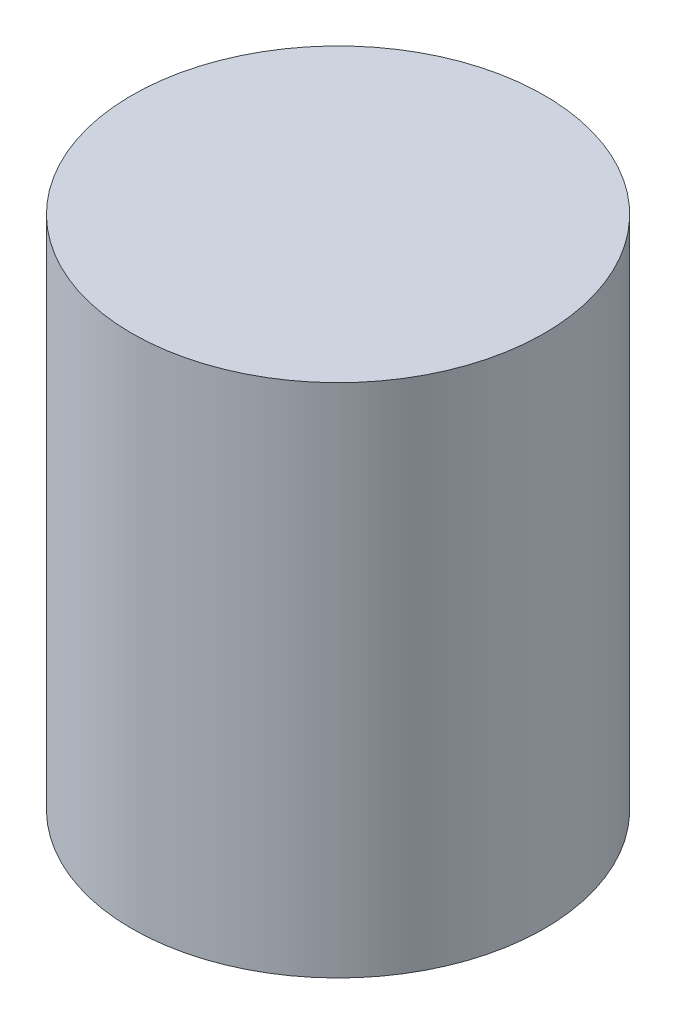
SolidWorks part; units mm, degrees
material "6061-T6 (SS)"
ref_plane "Front Plane" through (0, 0, 0) normal (0, 0, 1) x (1, 0, 0)
ref_plane "Top Plane" through (0, 0, 0) normal (0, 1, 0) x (1, 0, 0)
ref_plane "Right Plane" through (0, 0, 0) normal (1, 0, 0) x (0, 0, -1)
sketch "Sketch1" plane through (0, 0, 0) normal (0, 1, 0) x (1, 0, 0)
  circle A0 centre (0, 0) radius 4
  dimension "D1" = 8
extrude "Boss-Extrude1" add sketch "Sketch1" along normal mid plane 10
